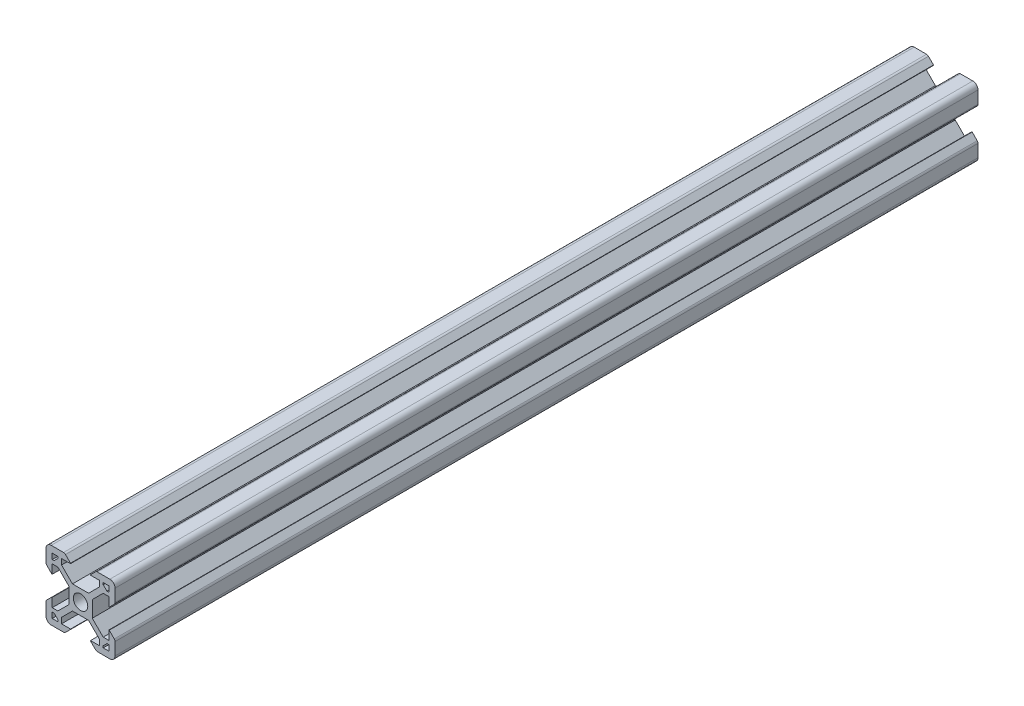
SolidWorks part; units mm, degrees
ref_plane "Front Plane" through (0, 0, 0) normal (0, 0, 1) x (1, 0, 0)
ref_plane "Top Plane" through (0, 0, 0) normal (0, 1, 0) x (1, 0, 0)
ref_plane "Right Plane" through (0, 0, 0) normal (1, 0, 0) x (0, 0, -1)
sketch "Sketch2" plane through (0, 0, 0) normal (0, 0, 1) x (1, 0, 0)
  line L0 (-8.2, 2.89) -> (-8.2, 5.5)
  line L1 (-2.1, 0) -> (-10, 0) construction
  line L2 (0, 2.1) -> (0, 10) construction
  line L3 (-4.9072, 10) -> (-8.5, 10)
  line L4 (-10, 4.9072) -> (-10, 8.5)
  line L5 (-2.1, 0) -> (-3.4, 0) construction
  line L6 (0, 2.1) -> (0, 3.4) construction
  line L7 (0, 3.4) -> (-2.3393, 3.4)
  line L8 (-3.4, 0) -> (-3.4, 2.3393)
  line L9 (-2.89, 8.2) -> (-5.5, 8.2)
  line L10 (-6.57, 8.2) -> (-6.57, 7.66)
  line L11 (-8.2, 6.57) -> (-7.66, 6.57)
  line L12 (-5.5, 8.2) -> (-5.5, 6.5607)
  line L13 (-6.5607, 5.5) -> (-8.2, 5.5)
  line L14 (-8.2, 8.2) -> (-1.4849, 1.4849) construction
  line L15 (-6.5607, 5.5) -> (-3.4, 2.3393)
  line L16 (-5.5, 6.5607) -> (-2.3393, 3.4)
  line L17 (-7.66, 6.57) -> (-6.57, 7.66)
  line L18 (-8.7303, 7.6697) -> (-0.5303, -0.5303) construction
  line L19 (-7.6697, 8.7303) -> (0.5303, 0.5303) construction
  line L20 (-8.2, 8.2) -> (0, 0) construction
  line L21 (-8.2, 6.57) -> (-8.2, 8.2)
  line L22 (-8.2, 0) -> (-8.2, 8.2) construction
  line L23 (-6.57, 8.2) -> (-8.2, 8.2)
  line L24 (0, 8.2) -> (-8.2, 8.2) construction
  line L25 (-10, 0) -> (-10, 10) construction
  line L26 (0, 10) -> (-10, 10) construction
  line L27 (-2.89, 8.31) -> (-2.89, 8.2)
  line L29 (-8.31, 2.89) -> (-8.2, 2.89)
  line L30 (-4.3486, 9.7686) -> (-2.89, 8.31)
  line L31 (-8.31, 2.89) -> (-9.7686, 4.3486)
  arc A0 (0, 2.1) -> (-2.1, 0) centre (0, 0) ccw
  arc A1 (-10, 8.5) -> (-8.5, 10) centre (-8.5, 8.5) cw
  arc A2 (-9.7686, 4.3486) -> (-10, 4.9072) centre (-9.21, 4.9072) cw
  arc A3 (-4.3486, 9.7686) -> (-4.9072, 10) centre (-4.9072, 9.21) ccw
  point P29 (-10, 10)
  point P39 (-10, 4.58)
  point P42 (-4.58, 10)
  dimension "D3" = 2.1
  dimension "D15" = 1.5
  dimension "D22" = 0.79
  dimension "D1" = 10
  dimension "D2" = 10
  dimension "D4" = 1.8
  dimension "D5" = 3.43
  dimension "D6" = 3.43
  dimension "D7" = 0.54
  dimension "D8" = 0.54
  dimension "D9" = 1.07
  dimension "D10" = 1.07
  dimension "D11" = 3.4
  dimension "D12" = 3.4
  dimension "D16" = 7.11
  dimension "D17" = 0.11
  dimension "D18" = 1.69
  dimension "D19" = 0.11
  dimension "D20" = 7.11
  dimension "D21" = 1.69
  dimension "D13" = 0.75
  dimension "D14" = 0.75
sketch "Sketch6" plane through (0, 0, 0) normal (0, 0, 1) x (1, 0, 0)
  line L0 (-3.4, 0) -> (-3.4, 2.3393) construction
  line L1 (-6.5607, 5.5) -> (-3.4, 2.3393) construction
  line L2 (-6.5607, 5.5) -> (-8.2, 5.5) construction
  line L3 (-8.2, 2.89) -> (-8.2, 5.5) construction
  line L4 (-8.31, 2.89) -> (-8.2, 2.89) construction
  line L5 (-7.66, 6.57) -> (-6.57, 7.66)
  line L6 (-6.57, 7.66) -> (-6.57, 8.2)
  line L7 (-6.57, 8.2) -> (-8.2, 8.2)
  line L8 (-8.2, 8.2) -> (-8.2, 6.57)
  line L9 (-8.2, 6.57) -> (-7.66, 6.57)
  line L10 (-7.66, 6.57) -> (-6.57, 7.66)
  line L11 (-6.57, 7.66) -> (-6.57, 8.2)
  line L12 (-6.57, 8.2) -> (-8.2, 8.2)
  line L13 (-8.2, 8.2) -> (-8.2, 6.57)
  line L14 (-8.2, 6.57) -> (-7.66, 6.57)
  line L15 (-8.31, 2.89) -> (-9.7686, 4.3486) construction
  line L16 (-10, 4.9072) -> (-10, 8.5) construction
  line L17 (-4.9072, 10) -> (-8.5, 10) construction
  line L18 (-4.3486, 9.7686) -> (-2.89, 8.31) construction
  line L19 (-2.89, 8.31) -> (-2.89, 8.2) construction
  line L20 (-2.89, 8.2) -> (-5.5, 8.2) construction
  line L21 (-5.5, 8.2) -> (-5.5, 6.5607) construction
  line L22 (-5.5, 6.5607) -> (-2.3393, 3.4) construction
  line L23 (0, 3.4) -> (-2.3393, 3.4) construction
  line L24 (-3.4, -2.3393) -> (-3.4, 2.3393)
  line L25 (-6.5607, 5.5) -> (-3.4, 2.3393)
  line L26 (-6.5607, 5.5) -> (-8.2, 5.5)
  line L27 (-8.2, 2.89) -> (-8.2, 5.5)
  line L28 (-8.31, 2.89) -> (-8.2, 2.89)
  line L29 (-8.31, 2.89) -> (-9.7686, 4.3486)
  line L30 (-10, 4.9072) -> (-10, 8.5)
  line L31 (-4.9072, 10) -> (-8.5, 10)
  line L32 (-4.3486, 9.7686) -> (-2.89, 8.31)
  line L33 (-2.89, 8.31) -> (-2.89, 8.2)
  line L34 (-2.89, 8.2) -> (-5.5, 8.2)
  line L35 (-5.5, 8.2) -> (-5.5, 6.5607)
  line L36 (-5.5, 6.5607) -> (-2.3393, 3.4)
  line L37 (2.3393, 3.4) -> (-2.3393, 3.4)
  line L38 (0, 2.1) -> (0, 10) construction
  line L39 (-2.1, 0) -> (-10, 0) construction
  line L40 (0, 2.1) -> (0, 10) construction
  line L41 (-2.1, 0) -> (-10, 0) construction
  line L42 (2.1, 0) -> (10, 0) construction
  line L43 (5.5, 6.5607) -> (2.3393, 3.4)
  line L44 (5.5, 8.2) -> (5.5, 6.5607)
  line L45 (2.89, 8.2) -> (5.5, 8.2)
  line L46 (2.89, 8.31) -> (2.89, 8.2)
  line L47 (4.3486, 9.7686) -> (2.89, 8.31)
  line L48 (4.9072, 10) -> (8.5, 10)
  line L49 (10, 4.9072) -> (10, 8.5)
  line L50 (8.31, 2.89) -> (9.7686, 4.3486)
  line L51 (8.31, 2.89) -> (8.2, 2.89)
  line L52 (8.2, 2.89) -> (8.2, 5.5)
  line L53 (6.5607, 5.5) -> (8.2, 5.5)
  line L54 (6.5607, 5.5) -> (3.4, 2.3393)
  line L55 (3.4, -2.3393) -> (3.4, 2.3393)
  line L56 (8.2, 6.57) -> (7.66, 6.57)
  line L57 (8.2, 8.2) -> (8.2, 6.57)
  line L58 (6.57, 8.2) -> (8.2, 8.2)
  line L59 (6.57, 7.66) -> (6.57, 8.2)
  line L60 (7.66, 6.57) -> (6.57, 7.66)
  line L61 (0, -2.1) -> (0, -10) construction
  line L62 (7.66, -6.57) -> (6.57, -7.66)
  line L63 (6.57, -7.66) -> (6.57, -8.2)
  line L64 (6.57, -8.2) -> (8.2, -8.2)
  line L65 (8.2, -8.2) -> (8.2, -6.57)
  line L66 (8.2, -6.57) -> (7.66, -6.57)
  line L67 (6.5607, -5.5) -> (3.4, -2.3393)
  line L68 (6.5607, -5.5) -> (8.2, -5.5)
  line L69 (8.2, -2.89) -> (8.2, -5.5)
  line L70 (8.31, -2.89) -> (8.2, -2.89)
  line L71 (8.31, -2.89) -> (9.7686, -4.3486)
  line L72 (10, -4.9072) -> (10, -8.5)
  line L73 (4.9072, -10) -> (8.5, -10)
  line L74 (4.3486, -9.7686) -> (2.89, -8.31)
  line L75 (2.89, -8.31) -> (2.89, -8.2)
  line L76 (2.89, -8.2) -> (5.5, -8.2)
  line L77 (5.5, -8.2) -> (5.5, -6.5607)
  line L78 (5.5, -6.5607) -> (2.3393, -3.4)
  line L79 (2.3393, -3.4) -> (-2.3393, -3.4)
  line L80 (-5.5, -6.5607) -> (-2.3393, -3.4)
  line L81 (-5.5, -8.2) -> (-5.5, -6.5607)
  line L82 (-2.89, -8.2) -> (-5.5, -8.2)
  line L83 (-2.89, -8.31) -> (-2.89, -8.2)
  line L84 (-4.3486, -9.7686) -> (-2.89, -8.31)
  line L85 (-4.9072, -10) -> (-8.5, -10)
  line L86 (-10, -4.9072) -> (-10, -8.5)
  line L87 (-8.31, -2.89) -> (-9.7686, -4.3486)
  line L88 (-8.31, -2.89) -> (-8.2, -2.89)
  line L89 (-8.2, -2.89) -> (-8.2, -5.5)
  line L90 (-6.5607, -5.5) -> (-8.2, -5.5)
  line L91 (-6.5607, -5.5) -> (-3.4, -2.3393)
  line L92 (-8.2, -6.57) -> (-7.66, -6.57)
  line L93 (-8.2, -8.2) -> (-8.2, -6.57)
  line L94 (-6.57, -8.2) -> (-8.2, -8.2)
  line L95 (-6.57, -7.66) -> (-6.57, -8.2)
  line L96 (-7.66, -6.57) -> (-6.57, -7.66)
  arc A0 (0, 2.1) -> (-2.1, 0) centre (0, 0) ccw construction
  arc A1 (-10, 4.9072) -> (-9.7686, 4.3486) centre (-9.21, 4.9072) ccw construction
  arc A2 (-8.5, 10) -> (-10, 8.5) centre (-8.5, 8.5) ccw construction
  arc A3 (-4.3486, 9.7686) -> (-4.9072, 10) centre (-4.9072, 9.21) ccw construction
  circle A4 centre (0, 0) radius 2.1
  arc A5 (-10, 4.9072) -> (-9.7686, 4.3486) centre (-9.21, 4.9072) ccw
  arc A6 (-8.5, 10) -> (-10, 8.5) centre (-8.5, 8.5) ccw
  arc A7 (-4.3486, 9.7686) -> (-4.9072, 10) centre (-4.9072, 9.21) ccw
  arc A8 (4.3486, 9.7686) -> (4.9072, 10) centre (4.9072, 9.21) cw
  arc A9 (8.5, 10) -> (10, 8.5) centre (8.5, 8.5) cw
  arc A10 (10, 4.9072) -> (9.7686, 4.3486) centre (9.21, 4.9072) cw
  arc A11 (10, -4.9072) -> (9.7686, -4.3486) centre (9.21, -4.9072) ccw
  arc A12 (8.5, -10) -> (10, -8.5) centre (8.5, -8.5) ccw
  arc A13 (4.3486, -9.7686) -> (4.9072, -10) centre (4.9072, -9.21) ccw
  arc A14 (-4.3486, -9.7686) -> (-4.9072, -10) centre (-4.9072, -9.21) cw
  arc A15 (-8.5, -10) -> (-10, -8.5) centre (-8.5, -8.5) cw
  arc A16 (-10, -4.9072) -> (-9.7686, -4.3486) centre (-9.21, -4.9072) cw
  point P85 (3.4, 0)
  dimension "D1" = 0
extrude "Boss-Extrude1" add sketch "Sketch6" against normal blind 250
ref_plane "Middle" through (0, 0, -125) normal (0, 0, 1) x (1, 0, 0)
